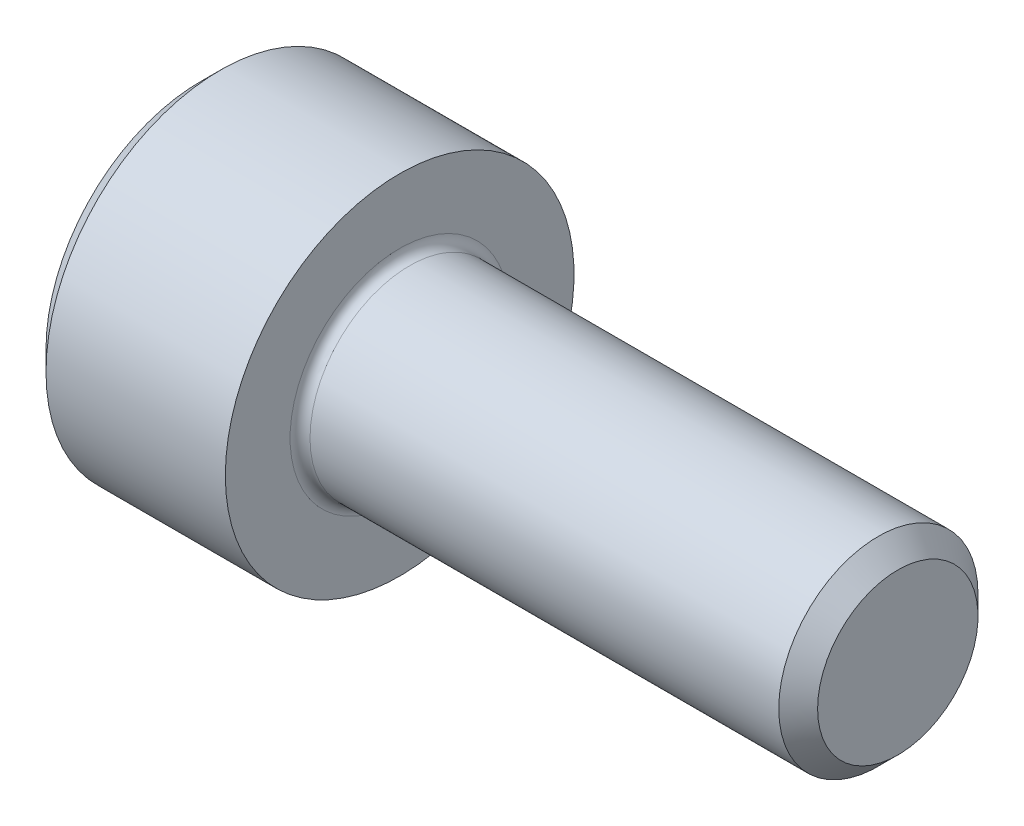
SolidWorks part; units mm, degrees
revolve "Base-Revolve" add sketch "BodySke"
sketch "BodySke" plane through (0, 0, 0) normal (0, 0, 1) x (1, 0, 0)
  line L0 (0, 0) -> (0, 3.1)
  line L1 (0.4, 3.5) -> (4, 3.5)
  line L2 (4, 3.5) -> (4, 2)
  line L3 (4, 2) -> (13.61, 2)
  line L4 (14, 1.61) -> (14, 0)
  line L5 (14, 0) -> (0, 0)
  line L6 (-31.75, 0) -> (127, 0) construction
  line L7 (0, 3.1) -> (0.4, 3.5)
  line L8 (14, 1.61) -> (13.61, 2)
  line L9 (0, -3.1) -> (0.4, -3.5) construction
  line L10 (14, -1.61) -> (13.61, -2) construction
  line L11 (4.7, 9.525) -> (4.7, 3.175) construction
  line L12 (4, 9.525) -> (4, 3.175) construction
  line L13 (-36, 9.525) -> (-36, 3.175) construction
  dimension "Diameter" = 4
  dimension "Head_ht" = 4
  dimension "Length" = 10
  dimension "Body_ch_ang" = 45
  dimension "Head_dia" = 7
  dimension "Head_ch_ang" = 45
  dimension "Minor_dia" = 3.22
  dimension "Advance" = 0.7
  dimension "Thread_nom" = 10
  dimension "Thread_length" = 50
  dimension "Head_ch_ht" = 0.4
cosmetic thread "ThreadCosmetic" [suppressed]
fillet "Fillet1" radius 0.2 1 edges at (4, 0, 2)
ref_plane "Plane1" through (0, 0, 0) normal (0, 0, 1) x (1, 0, 0)
ref_plane "Plane2" through (0, 0, 0) normal (0, 1, 0) x (1, 0, 0)
ref_plane "Plane3" through (0, 0, 0) normal (1, 0, 0) x (0, 0, -1)
sketch "Sketch2" plane through (0, 0, 0) normal (0, 0, 1) x (1, 0, 0)
  line L0 (0, 1.5355) -> (2, 1.5355)
  line L1 (2, 1.5355) -> (2.8865, 0)
  line L2 (-31.75, 0) -> (127, 0) construction
  line L3 (2.8865, 0) -> (0, 0)
  line L4 (0, 0) -> (0, 1.5355)
  line L5 (0, 3.1) -> (0, -3.1) construction
  line L6 (0, 0) -> (47.625, 0) construction
  line L7 (4, -3.5) -> (4, 3.5) construction
  dimension "D1" = 1.5355
  dimension "D2" = 60
revolve "Hex-PreBroach" cut sketch "Sketch2" angle 360 about L6
sketch "Sketch3" plane through (0, 0, 0) normal (-1, 0, 0) x (0, 0.5, 0.866)
  line L0 (0.8865, 1.5355) -> (-0.8865, 1.5355)
  line L1 (-0.8865, 1.5355) -> (-1.773, 0)
  line L2 (0.8865, 1.5355) -> (1.773, 0)
  line L3 (0.8865, -1.5355) -> (1.773, 0)
  line L4 (0.8865, -1.5355) -> (-0.8865, -1.5355)
  line L5 (-0.8865, -1.5355) -> (-1.773, 0)
  dimension "D1" = 1.5355
  dimension "D2" = 1.5355
  dimension "Hex_size" = 3.071
extrude "Hex" cut sketch "Sketch3" against normal blind 2
sketch "Sketch4" plane through (0, 0, 0) normal (-1, 0, 0) x (0, 0, 1)
  line L0 (0, 0) -> (1.7399, 0)
  line L1 (0, 0) -> (6.1484, 3.5498) construction
  line L2 (0, 0) -> (0.8699, 1.5068)
  line L3 (1.4457, 0.3947) -> (1.6607, 0.5189)
  line L4 (1.0647, 1.0546) -> (1.2797, 1.1788)
  arc A0 (1.4457, 0.3947) -> (1.0647, 1.0546) centre (0, 0) ccw
  arc A1 (1.7399, 0) -> (1.6607, 0.5189) centre (0, 0) ccw
  arc A2 (0.8699, 1.5068) -> (1.2797, 1.1788) centre (0, 0) cw
  dimension "D1" = 30
  dimension "D2" = 60
  dimension "Spline_p_dim" = 0.762
  dimension "D3" = 0.381
extrude "Spline" [suppressed] cut sketch "Sketch4" against normal blind 2
pattern_circular "CirPattern1" [suppressed] count 6 every 60
sketch "Sketch5" plane through (0, 0, 0) normal (0, 0, 1) x (1, 0, 0)
  line L0 (-31.75, 0) -> (127, 0) construction
  line L2 (0, 3.1) -> (0, -3.1) construction
  circle A0 centre (1.6, 0) radius 0.675
  dimension "Drilled_hole_dia" = 1.35
  dimension "Drilled_hole_loc" = 1.6
extrude "Hole" [suppressed] cut sketch "Sketch5" against normal through all and the other way through all
pattern_circular "Drilled-4" [suppressed] count 2 every 60
pattern_circular "Drilled-6" [suppressed] count 3 every 60
sketch "ThdSchSke" plane through (0, 0, 0) normal (0, 0, 1) x (1, 0, 0)
  line L0 (4.7, -1.61) -> (4.4269, -2)
  line L1 (4.7, -1.61) -> (4.9731, -2)
  line L2 (4.9731, -2) -> (4.9731, -2.5)
  line L3 (-3.175, 0) -> (5.1513, 0) construction
  line L5 (4.9731, -2.5) -> (4.4269, -2.5)
  line L6 (4.4269, -2.5) -> (4.4269, -2)
  line L7 (0, 3.1) -> (0, -3.1) construction
  dimension "Thread_minor" = 3.22
  dimension "Diameter" = 4
  dimension "Start" = 4.7
revolve "ThreadSchematic" [suppressed] cut sketch "ThdSchSke" angle 360 about L3
pattern_linear "ThdSchPat" [suppressed]
equation "\"D2@Sketch3\" = \"Hex_size@Sketch3\" / 2"
equation "\"D1@Sketch3\" = \"Hex_size@Sketch3\" / 2"
equation "\"D1@Sketch2\" = \"Hex_size@Sketch3\" / 2"
equation "\"D3@Sketch4\" = \"Spline_p_dim@Sketch4\" / 2"
equation "\"Thread_minor@ThreadCosmetic\"  =  \"Minor_dia@BodySke\""
equation "\"D2@CirPattern1\" = 360 / \"Num_teeth@CirPattern1\""
equation "\"Wall_thickness@Sketch2\" = \"Head_ht@BodySke\" - \"Key_eng@Hex\""
equation "\"Thread_length@ThreadCosmetic\" = ((sgn( (\"Length@BodySke\" - \"Advance@BodySke\" ) - \"Thread_nom@BodySke\" )-1)*( (\"Length@BodySke\" - \"Advance@BodySke\" ) - \"Thread_nom@BodySke\" ))/-2+ \"Thread_nom@BodySke\""
equation "\"Thread_minor@ThdSchSke\" = \"Minor_dia@BodySke\""
equation "\"Diameter@ThdSchSke\" = \"Diameter@BodySke\""
equation "\"Overcut@ThdSchSke\" = \"Diameter@BodySke\" * 1.25"
equation "\"Start@ThdSchSke\" = \"Head_ht@BodySke\" + \"Length@BodySke\" - \"Thread_length@ThreadCosmetic\"  '---Non-countersunk---"
equation "\"Num_threads@ThdSchPat\" = int( \"Thread_length@ThreadCosmetic\" / \"Advance@BodySke\" + 0.999 )  + 1"
equation "\"Advance@ThdSchPat\" = \"Thread_length@ThreadCosmetic\" /  (\"Num_threads@ThdSchPat\" - 1) 'relax it"
equation "\"Num_threads@ThdSchPat\" = \"Num_threads@ThdSchPat\" - sgn( \"Num_threads@ThdSchPat\" - 1) '---chamfered tips only---"
